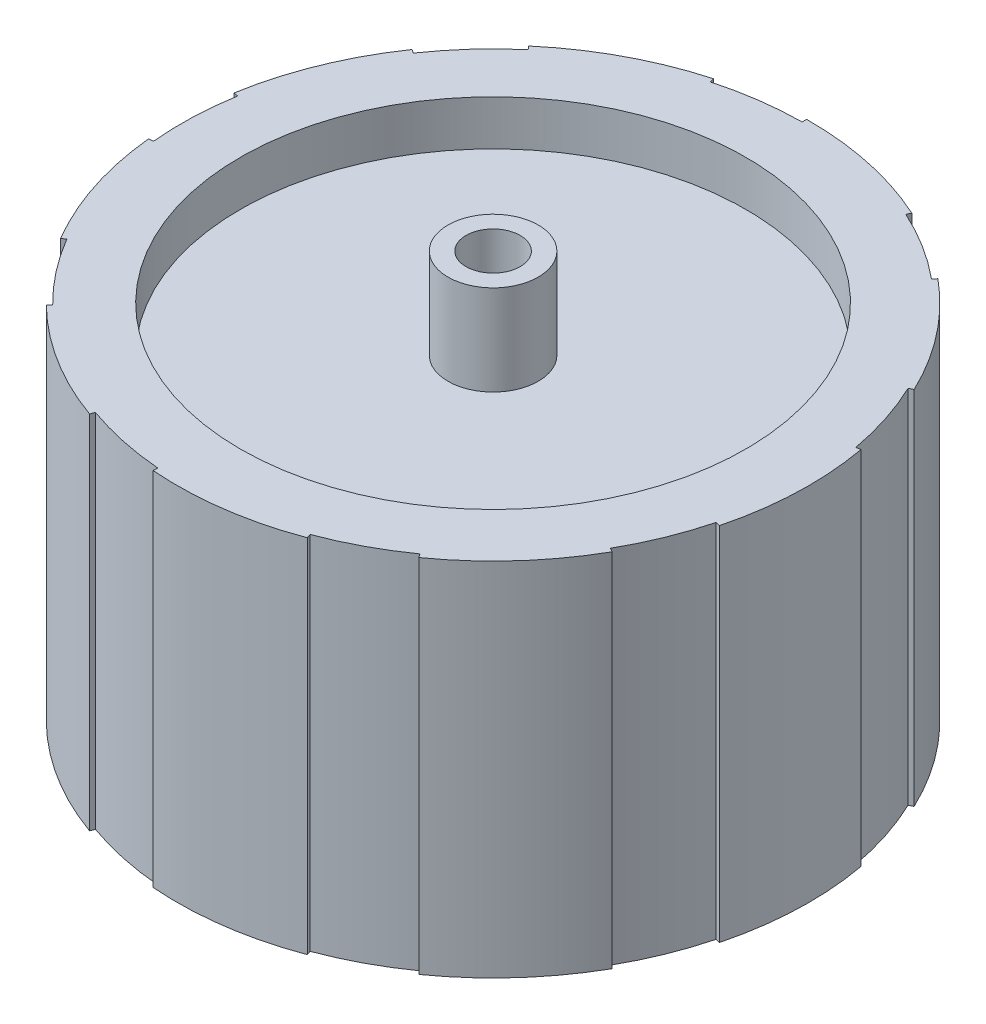
SolidWorks part; units mm, degrees
ref_plane "Front Plane" through (0, 0, 0) normal (0, 0, 1) x (1, 0, 0)
ref_plane "Top Plane" through (0, 0, 0) normal (0, 1, 0) x (1, 0, 0)
ref_plane "Right Plane" through (0, 0, 0) normal (1, 0, 0) x (0, 0, -1)
sketch "Sketch1" plane through (0, 0, 0) normal (0, 1, 0) x (1, 0, 0)
  line L0 (-9.1837, 33.2552) -> (-9.3168, 33.7372) construction
  line L1 (-0.2637, 34.499) -> (-0.2675, 34.999) construction
  line L2 (-9.3168, 33.7372) -> (-9.1837, 33.2552)
  line L3 (-7.3702, 35.783) -> (-7.3702, 35.805)
  line L4 (-0.2675, 34.999) -> (-0.2637, 34.499)
  line L5 (-0.2637, 34.499) -> (-0.2417, 34.4367)
  line L6 (22.292, 26.9827) -> (21.9735, 26.5973)
  line L7 (14.5488, 31.8329) -> (14.3409, 31.3781)
  line L8 (34.4208, 6.3409) -> (33.9291, 6.2504)
  line L9 (31.6068, 15.0336) -> (31.1553, 14.8189)
  line L10 (30.4438, -17.2678) -> (30.0088, -17.0211)
  line L11 (33.8757, -8.8) -> (33.3917, -8.6743)
  line L12 (12.2217, -32.7968) -> (12.0471, -32.3283)
  line L13 (20.2937, -28.5161) -> (20.0038, -28.1087)
  line L14 (-11.719, -32.9798) -> (-11.5516, -32.5086)
  line L15 (-2.7839, -34.8891) -> (-2.7441, -34.3907)
  line L16 (-30.1763, -17.7312) -> (-29.7452, -17.4778)
  line L17 (-24.5589, -24.9372) -> (-24.208, -24.5809)
  line L18 (-34.5137, 5.8141) -> (-34.0207, 5.731)
  line L19 (-34.8425, -3.3168) -> (-34.3447, -3.2695)
  line L20 (-22.7018, 26.6388) -> (-22.3775, 26.2583)
  line L21 (-28.8229, 19.8555) -> (-28.4112, 19.5718)
  arc A0 (-9.3168, 33.7372) -> (-22.7018, 26.6388) centre (0, 0) ccw
  arc A1 (-0.2637, 34.499) -> (-9.1837, 33.2552) centre (0, 0) ccw
  arc A2 (21.9735, 26.5973) -> (14.3409, 31.3781) centre (0, 0) ccw
  arc A3 (33.9291, 6.2504) -> (31.1553, 14.8189) centre (0, 0) ccw
  arc A4 (30.0088, -17.0211) -> (33.3917, -8.6743) centre (0, 0) ccw
  arc A5 (12.0471, -32.3283) -> (20.0038, -28.1087) centre (0, 0) ccw
  arc A6 (-11.5516, -32.5086) -> (-2.7441, -34.3907) centre (0, 0) ccw
  arc A7 (-29.7452, -17.4778) -> (-24.208, -24.5809) centre (0, 0) ccw
  arc A8 (-34.0207, 5.731) -> (-34.3447, -3.2695) centre (0, 0) ccw
  arc A9 (-22.3775, 26.2583) -> (-28.4112, 19.5718) centre (0, 0) ccw
  arc A10 (20.2937, -28.5161) -> (30.4438, -17.2678) centre (0, 0) ccw
  arc A11 (33.8757, -8.8) -> (34.4208, 6.3409) centre (0, 0) ccw
  arc A12 (31.6068, 15.0336) -> (22.292, 26.9827) centre (0, 0) ccw
  arc A13 (14.5488, 31.8329) -> (-0.2675, 34.999) centre (0, 0) ccw
  arc A14 (-28.8229, 19.8555) -> (-34.5137, 5.8141) centre (0, 0) ccw
  arc A15 (-34.8425, -3.3168) -> (-30.1763, -17.7312) centre (0, 0) ccw
  arc A16 (-24.5589, -24.9372) -> (-11.719, -32.9798) centre (0, 0) ccw
  arc A17 (-2.7839, -34.8891) -> (12.2217, -32.7968) centre (0, 0) ccw
  point P44 (0, 0)
  dimension "D1" = 15
  dimension "D2" = 9
extrude "Boss-Extrude1" add sketch "Sketch1" along normal blind 40
sketch "Sketch2" plane through (0, 40, 0) normal (0, 1, 0) x (1, 0, 0)
  circle A0 centre (0, 0) radius 28
extrude "Cut-Extrude1" cut sketch "Sketch2" against normal blind 5
sketch "Sketch3" plane through (0, 0, 0) normal (0, -1, 0) x (1, 0, 0)
  circle A0 centre (0, 0) radius 28
extrude "Cut-Extrude2" cut sketch "Sketch3" against normal blind 5
sketch "Sketch4" plane through (0, 35, 0) normal (0, 1, 0) x (1, 0, 0)
  circle A0 centre (0, 0) radius 5
extrude "Boss-Extrude2" add sketch "Sketch4" along normal blind 10
sketch "Sketch5" plane through (0, 5, 0) normal (0, -1, 0) x (1, 0, 0)
  circle A0 centre (0, 0) radius 5
extrude "Boss-Extrude3" add sketch "Sketch5" along normal blind 10
sketch "Sketch6" plane through (0, -5, 0) normal (0, -1, 0) x (1, 0, 0)
  circle A0 centre (0, 0) radius 3
extrude "Cut-Extrude3" cut sketch "Sketch6" against normal through all
